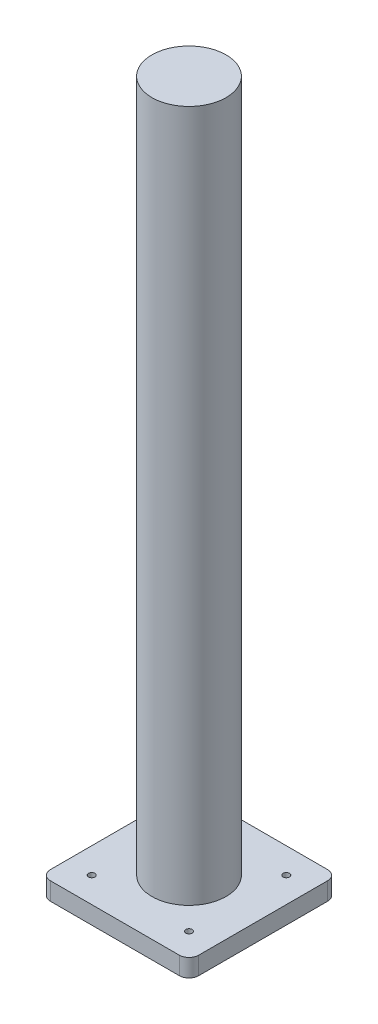
SolidWorks part; units mm, degrees
ref_plane "Front Plane" through (0, 0, 0) normal (0, 0, 1) x (1, 0, 0)
ref_plane "Top Plane" through (0, 0, 0) normal (0, 1, 0) x (1, 0, 0)
ref_plane "Right Plane" through (0, 0, 0) normal (1, 0, 0) x (0, 0, -1)
sketch "Sketch1" plane through (0, 0, 0) normal (0, 1, 0) x (1, 0, 0)
  line L1 (0, 0) -> (76.2, 0)
  line L2 (0, 0) -> (0, 76.2)
  line L3 (0, 76.2) -> (76.2, 76.2)
  line L4 (76.2, 0) -> (76.2, 76.2)
  dimension "D1" = 76.2
  dimension "D2" = 76.2
extrude "Boss-Extrude1" add sketch "Sketch1" along normal blind 9.144
sketch "Sketch2" plane through (0, 9.144, 0) normal (0, 1, 0) x (1, 0, 0)
  line L0 (38.1, 76.2) -> (38.1, 0) construction
  line L1 (76.2, 76.2) -> (0, 76.2) construction
  line L2 (0, 0) -> (76.2, 0) construction
  line L3 (0, 38.1) -> (76.2, 38.1) construction
  line L4 (0, 76.2) -> (0, 0) construction
  line L5 (76.2, 0) -> (76.2, 76.2) construction
  line L7 (13.1, 13.1) -> (63.1, 13.1) construction
  line L8 (13.1, 13.1) -> (13.1, 63.1) construction
  line L9 (13.1, 63.1) -> (63.1, 63.1) construction
  line L10 (63.1, 13.1) -> (63.1, 63.1) construction
  line L11 (13.1, 13.1) -> (63.1, 63.1) construction
  line L12 (13.1, 63.1) -> (63.1, 13.1) construction
  circle A0 centre (13.1, 63.1) radius 1.65
  circle A1 centre (63.1, 63.1) radius 1.65
  circle A2 centre (63.1, 13.1) radius 1.65
  circle A3 centre (13.1, 13.1) radius 1.65
  point P12 (38.1, 38.1)
  dimension "D3" = 3.3
  dimension "D4" = 3.3
  dimension "D5" = 3.3
  dimension "D6" = 3.3
  dimension "D1" = 50
  dimension "D2" = 50
extrude "Cut-Extrude1" cut sketch "Sketch2" against normal blind 9.144
sketch "Sketch3" plane through (0, 9.144, 0) normal (0, 1, 0) x (1, 0, 0)
  line L0 (38.1, 76.2) -> (38.1, 0) construction
  line L1 (76.2, 76.2) -> (0, 76.2) construction
  line L2 (0, 0) -> (76.2, 0) construction
  line L3 (0, 38.1) -> (76.2, 38.1) construction
  line L4 (0, 76.2) -> (0, 0) construction
  line L5 (76.2, 0) -> (76.2, 76.2) construction
  circle A0 centre (38.1, 38.1) radius 19.05
  dimension "D1" = 38.1
extrude "Boss-Extrude2" add sketch "Sketch3" along normal blind 355.6
fillet "Fillet1" radius 5 4 edges at (0, 4.572, -76.2) (76.2, 4.572, -76.2) (76.2, 4.572, 0) (0, 4.572, 0)
